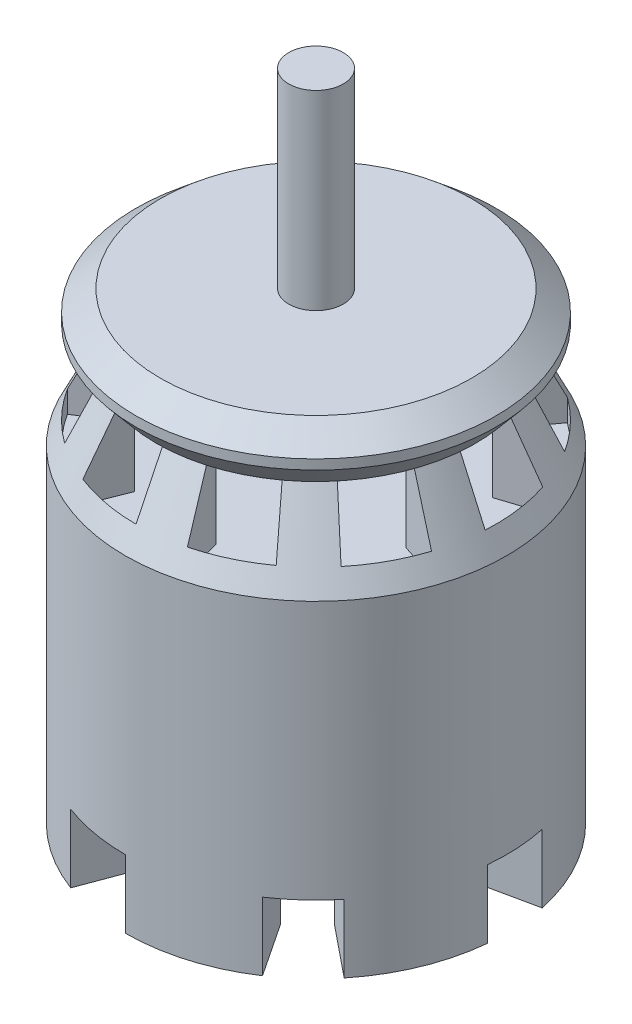
SolidWorks part; units mm, degrees
ref_plane "Front Plane" through (0, 0, 0) normal (0, 0, 1) x (1, 0, 0)
ref_plane "Top Plane" through (0, 0, 0) normal (0, 1, 0) x (1, 0, 0)
ref_plane "Right Plane" through (0, 0, 0) normal (1, 0, 0) x (0, 0, -1)
sketch "Sketch1" plane through (0, 0, 0) normal (0, 1, 0) x (1, 0, 0)
  circle A0 centre (0, 0) radius 14
  dimension "D1" = 28
extrude "Boss-Extrude1" add sketch "Sketch1" along normal blind 25
chamfer "Chamfer1" distance 6 angle 26 1 edges at (0, 25, 14)
sketch "Sketch2" plane through (0, 25, 0) normal (0, 1, 0) x (1, 0, 0)
  line L0 (0, 10.2912) -> (0, 13.2127)
  line L1 (0, 0) -> (3.746, 9.5852) construction
  line L2 (3.746, 9.5852) -> (4.8094, 12.3063)
  arc A0 (4.8094, 12.3063) -> (0, 13.2127) centre (0, 0) ccw
  arc A2 (0, 10.2912) -> (3.746, 9.5852) centre (0, 0) ccw
extrude "Cut-Extrude1" cut sketch "Sketch2" against normal blind 6
pattern_circular "CirPattern1" count 10 every 36 about axis through (0, 0, 0) along (0, 1, 0) of "Cut-Extrude1"
sketch "Sketch3" plane through (0, 25, 0) normal (0, 1, 0) x (1, 0, 0)
  circle A0 centre (0, 0) radius 13.2127
extrude "Boss-Extrude2" add sketch "Sketch3" along normal blind 4
chamfer "Chamfer2" distance 1.5 angle 50 2 edges at (0, 25, 13.2127) (0, 29, 13.2127)
sketch "Sketch4" plane through (0, 19, 0) normal (0, 1, 0) x (1, 0, 0)
  circle A0 centre (0, 0) radius 2
  dimension "D1" = 4
extrude "Boss-Extrude3" add sketch "Sketch4" along normal blind 24
sketch "Sketch5" plane through (0, 0, 0) normal (0, -1, 0) x (1, 0, 0)
  line L0 (0, 9.3081) -> (0, 14)
  line L2 (5.1449, 7.7569) -> (7.7383, 11.667)
  arc A0 (7.7383, 11.667) -> (0, 14) centre (0, 0) ccw
  arc A1 (5.1449, 7.7569) -> (0, 9.3081) centre (0, 0) ccw
extrude "Boss-Extrude4" add sketch "Sketch5" along normal blind 5
pattern_circular "CirPattern2" count 7 every 51 about axis through (0, 0, 0) along (0, 1, 0) of "Boss-Extrude4"
